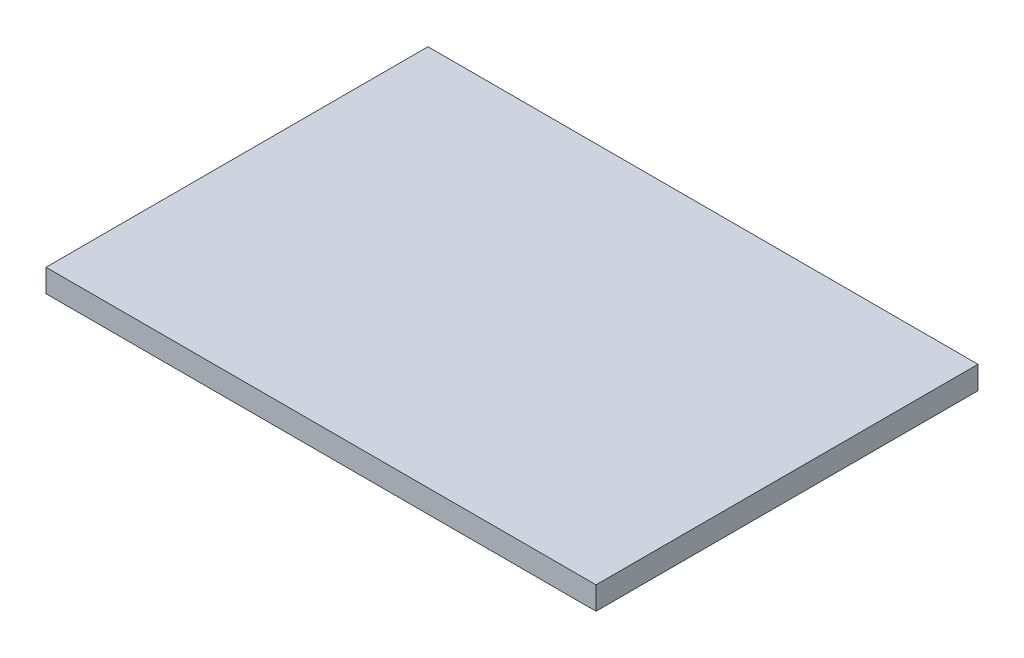
SolidWorks part; units mm, degrees
ref_plane "前视基准面" through (0, 0, 0) normal (0, 0, 1) x (1, 0, 0)
ref_plane "上视基准面" through (0, 0, 0) normal (0, 1, 0) x (1, 0, 0)
ref_plane "右视基准面" through (0, 0, 0) normal (1, 0, 0) x (0, 0, -1)
sketch "草图1" plane through (0, 0, 0) normal (0, 1, 0) x (1, 0, 0)
  line L1 (-36, 25) -> (36, 25)
  line L2 (-36, 25) -> (-36, -25)
  line L3 (-36, -25) -> (36, -25)
  line L4 (36, 25) -> (36, -25)
  line L5 (-36, 25) -> (36, -25) construction
  line L6 (-36, -25) -> (36, 25) construction
  point P0 (0, 0)
  dimension "D1" = 50
  dimension "D2" = 72
extrude "凸台-拉伸1" add sketch "草图1" along normal blind 3
